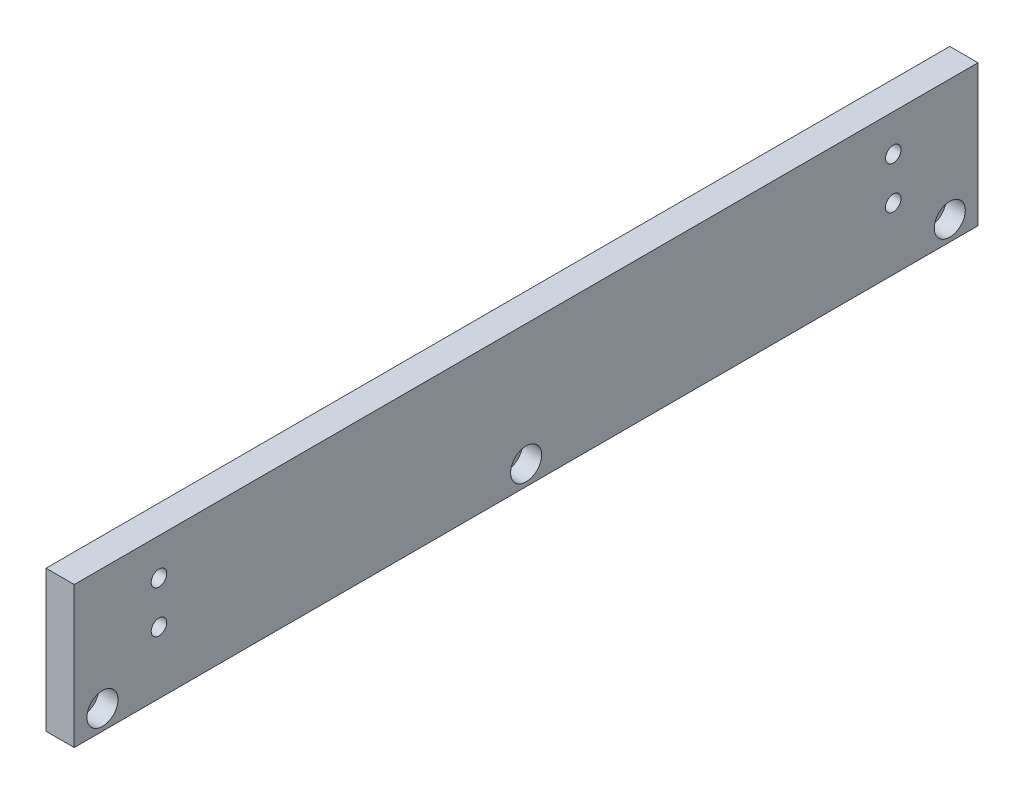
SolidWorks part; units mm, degrees
material "A3钢"
ref_plane "前视基准面" through (0, 0, 0) normal (0, 0, 1) x (1, 0, 0)
ref_plane "上视基准面" through (0, 0, 0) normal (0, 1, 0) x (1, 0, 0)
ref_plane "右视基准面" through (0, 0, 0) normal (1, 0, 0) x (0, 0, -1)
sketch "草图1" plane through (0, 0, 0) normal (0, 0, 1) x (1, 0, 0)
  line L0 (-58.1749, 0) -> (53.5621, 0) construction
  line L1 (0, 19.1787) -> (0, -27.9938) construction
  line L2 (0, 0) -> (10, 0)
  line L3 (10, 0) -> (10, 50)
  line L4 (10, 50) -> (0, 50)
  line L5 (0, 50) -> (0, 0)
  dimension "D3" = 50
  dimension "D4" = 10
extrude "凸台-拉伸1" add sketch "草图1" along normal blind 320
sketch "草图3" plane through (0, 0, 0) normal (-1, 0, 0) x (0, 0, 1)
  line L0 (320, 0) -> (320, 50) construction
  line L3 (320, 50) -> (0, 50) construction
  line L4 (30, 37) -> (290, 37)
  line L5 (30, 37) -> (30, 22)
  line L6 (30, 22) -> (290, 22)
  line L7 (290, 37) -> (290, 22)
  line L8 (30, 37) -> (290, 22) construction
  line L9 (30, 22) -> (290, 37) construction
  dimension "D3" = 30
  dimension "D4" = 13
  dimension "D1" = 260
  dimension "D2" = 15
sketch "草图7" plane through (10, 0, 0) normal (1, 0, 0) x (0, 0, -1)
  line L0 (-160, 50) -> (-160, -23.9428) construction
  line L1 (-320, 50) -> (0, 50) construction
  line L2 (-310, 7) -> (-160, 7) construction
  line L3 (-160, 7) -> (-10, 7) construction
  line L4 (-320, 0) -> (0, 0) construction
  dimension "D1" = 7
  dimension "D2" = 150
  dimension "D3" = 150
hole_wizard "打孔尺寸(%根据)内六角圆柱头螺钉的类型2" positions "3D草图1" profile "草图9" counterbore size "M6" standard "GB" end condition through all
sketch3d "3D草图1"
  point P0 (10, 7, 310)
  point P3 (10, 7, 160)
  point P6 (10, 7, 10)
sketch "草图9" plane through (10, 7, 310) normal (0, 1, 0) x (0, 0, -1)
  line L0 (0, 0) -> (0, 10)
  line L1 (0, 10) -> (3.3, 10)
  line L3 (3.3, 10) -> (3.3, 6.8)
  line L4 (3.3, 6.8) -> (5.5, 6.8)
  line L5 (5.5, 6.8) -> (5.5, 0)
  line L7 (5.5, 0) -> (0, 0)
  line L11 (0, -6.35) -> (0, 107.95) construction
  dimension "通孔孔直径" = 6.6
  dimension "通孔孔深度" = 10
  dimension "柱形沉头孔直径" = 11
  dimension "柱形沉头孔深度" = 6.8
hole_wizard "打孔尺寸(%根据)内六角圆柱头螺钉的类型2" positions "3D草图2" profile "草图10" counterbore size "M5" standard "GB" end condition through all
sketch3d "3D草图2"
  point P0 (0, 37, 290)
  point P3 (0, 22, 290)
  point P6 (0, 37, 30)
  point P9 (0, 22, 30)
sketch "草图10" plane through (0, 37, 290) normal (0, 1, 0) x (0, 0, 1)
  line L0 (0, 0) -> (0, 10)
  line L1 (0, 10) -> (2.75, 10)
  line L3 (2.75, 10) -> (2.75, 5.7)
  line L4 (2.75, 5.7) -> (5, 5.7)
  line L5 (5, 5.7) -> (5, 0)
  line L7 (5, 0) -> (0, 0)
  line L11 (0, -6.35) -> (0, 107.95) construction
  dimension "通孔孔直径" = 5.5
  dimension "通孔孔深度" = 10
  dimension "柱形沉头孔直径" = 10
  dimension "柱形沉头孔深度" = 5.7
